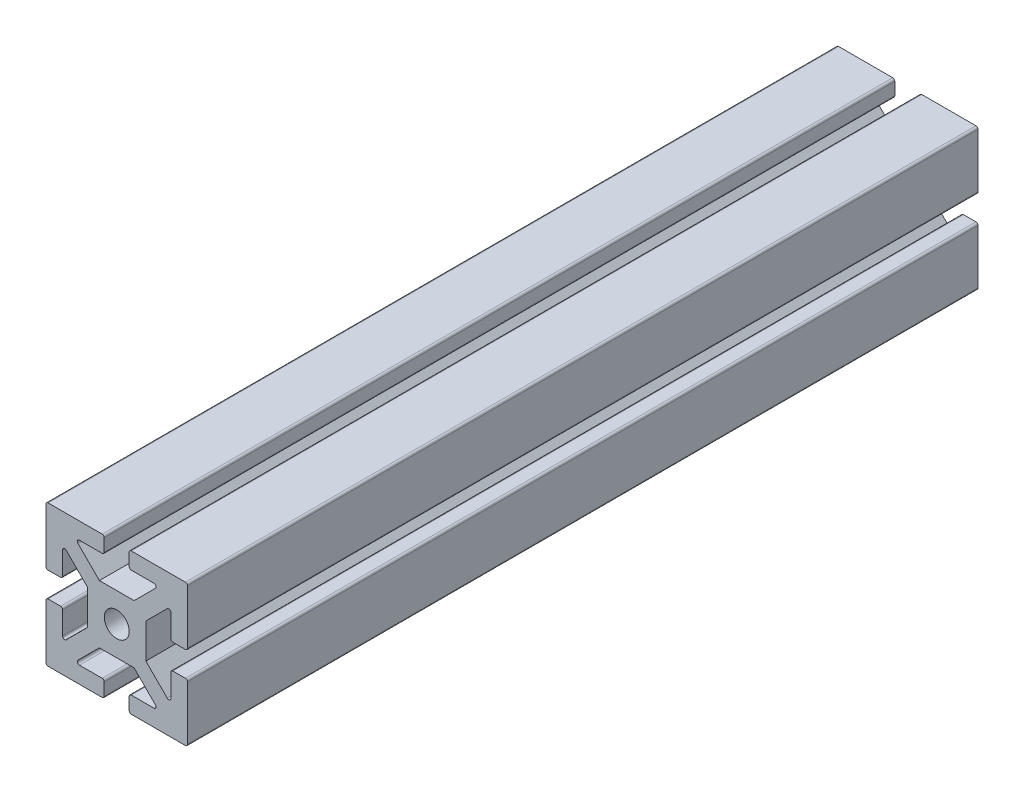
SolidWorks part; units mm, degrees
material "6061-T4 (SS)"
ref_plane "Front Plane" through (0, 0, 0) normal (0, 0, 1) x (1, 0, 0)
ref_plane "Top Plane" through (0, 0, 0) normal (0, 1, 0) x (1, 0, 0)
ref_plane "Right Plane" through (0, 0, 0) normal (1, 0, 0) x (0, 0, -1)
sketch "Sketch1" plane through (0, 0, 0) normal (0, 0, 1) x (1, 0, 0)
  line L0 (0, 0) -> (0, 14927.8117) construction
  line L1 (0, 0) -> (14927.8117, 0) construction
  line L2 (-2.0858, 3.5) -> (2.0858, 3.5)
  line L3 (2.0858, 3.5) -> (4.659, 6.0732)
  line L4 (4.4822, 6.5) -> (1.75, 6.5)
  line L5 (1.5, 6.75) -> (1.5, 8.25)
  line L6 (1.75, 8.5) -> (8.25, 8.5)
  line L7 (8.5, 8.25) -> (8.5, 1.75)
  line L8 (8.25, 1.5) -> (6.75, 1.5)
  line L9 (6.5, 1.75) -> (6.5, 4.4822)
  line L10 (6.0732, 4.659) -> (3.5, 2.0858)
  line L11 (3.5, 2.0858) -> (3.5, -2.0858)
  line L12 (6.0732, -4.659) -> (3.5, -2.0858)
  line L13 (6.5, -1.75) -> (6.5, -4.4822)
  line L14 (8.25, -1.5) -> (6.75, -1.5)
  line L15 (8.5, -8.25) -> (8.5, -1.75)
  line L16 (1.75, -8.5) -> (8.25, -8.5)
  line L17 (1.5, -6.75) -> (1.5, -8.25)
  line L18 (4.4822, -6.5) -> (1.75, -6.5)
  line L19 (2.0858, -3.5) -> (4.659, -6.0732)
  line L20 (-2.0858, -3.5) -> (2.0858, -3.5)
  line L21 (-2.0858, -3.5) -> (-4.659, -6.0732)
  line L22 (-4.4822, -6.5) -> (-1.75, -6.5)
  line L23 (-1.5, -6.75) -> (-1.5, -8.25)
  line L24 (-1.75, -8.5) -> (-8.25, -8.5)
  line L25 (-8.5, -8.25) -> (-8.5, -1.75)
  line L26 (-8.25, -1.5) -> (-6.75, -1.5)
  line L27 (-6.5, -1.75) -> (-6.5, -4.4822)
  line L28 (-6.0732, -4.659) -> (-3.5, -2.0858)
  line L29 (-3.5, 2.0858) -> (-3.5, -2.0858)
  line L30 (-6.0732, 4.659) -> (-3.5, 2.0858)
  line L31 (-6.5, 1.75) -> (-6.5, 4.4822)
  line L32 (-8.25, 1.5) -> (-6.75, 1.5)
  line L33 (-8.5, 8.25) -> (-8.5, 1.75)
  line L34 (-1.75, 8.5) -> (-8.25, 8.5)
  line L35 (-1.5, 6.75) -> (-1.5, 8.25)
  line L36 (-4.4822, 6.5) -> (-1.75, 6.5)
  line L37 (-2.0858, 3.5) -> (-4.659, 6.0732)
  circle A0 centre (0, 0) radius 1.5
  arc A1 (1.75, 6.5) -> (1.5, 6.75) centre (1.75, 6.75) cw
  arc A2 (1.5, 8.25) -> (1.75, 8.5) centre (1.75, 8.25) cw
  arc A3 (-1.75, 8.5) -> (-1.5, 8.25) centre (-1.75, 8.25) cw
  arc A4 (8.5, -8.25) -> (8.25, -8.5) centre (8.25, -8.25) cw
  arc A5 (8.25, -1.5) -> (8.5, -1.75) centre (8.25, -1.75) cw
  arc A6 (6.5, -1.75) -> (6.75, -1.5) centre (6.75, -1.75) cw
  arc A7 (6.0732, -4.659) -> (6.5, -4.4822) centre (6.25, -4.4822) ccw
  arc A8 (4.4822, -6.5) -> (4.659, -6.0732) centre (4.4822, -6.25) ccw
  arc A9 (1.75, -8.5) -> (1.5, -8.25) centre (1.75, -8.25) cw
  arc A10 (1.5, -6.75) -> (1.75, -6.5) centre (1.75, -6.75) cw
  arc A11 (-1.5, -8.25) -> (-1.75, -8.5) centre (-1.75, -8.25) cw
  arc A12 (-1.75, -6.5) -> (-1.5, -6.75) centre (-1.75, -6.75) cw
  arc A13 (-4.659, -6.0732) -> (-4.4822, -6.5) centre (-4.4822, -6.25) ccw
  arc A14 (-8.25, -8.5) -> (-8.5, -8.25) centre (-8.25, -8.25) cw
  arc A15 (-6.5, -4.4822) -> (-6.0732, -4.659) centre (-6.25, -4.4822) ccw
  arc A16 (-8.5, -1.75) -> (-8.25, -1.5) centre (-8.25, -1.75) cw
  arc A17 (-6.75, -1.5) -> (-6.5, -1.75) centre (-6.75, -1.75) cw
  arc A18 (-6.5, 1.75) -> (-6.75, 1.5) centre (-6.75, 1.75) cw
  arc A19 (-8.25, 1.5) -> (-8.5, 1.75) centre (-8.25, 1.75) cw
  arc A20 (-8.5, 8.25) -> (-8.25, 8.5) centre (-8.25, 8.25) cw
  arc A21 (-6.0732, 4.659) -> (-6.5, 4.4822) centre (-6.25, 4.4822) ccw
  arc A22 (-4.4822, 6.5) -> (-4.659, 6.0732) centre (-4.4822, 6.25) ccw
  arc A23 (-1.5, 6.75) -> (-1.75, 6.5) centre (-1.75, 6.75) cw
  arc A24 (4.659, 6.0732) -> (4.4822, 6.5) centre (4.4822, 6.25) ccw
  arc A25 (6.5, 4.4822) -> (6.0732, 4.659) centre (6.25, 4.4822) ccw
  arc A26 (6.75, 1.5) -> (6.5, 1.75) centre (6.75, 1.75) cw
  arc A27 (8.5, 1.75) -> (8.25, 1.5) centre (8.25, 1.75) cw
  arc A28 (8.25, 8.5) -> (8.5, 8.25) centre (8.25, 8.25) cw
  point P3 (-2.8019, 0.8886)
  point P19 (3.5, 0)
  point P29 (0, -3.5)
  point P46 (0, 3.5)
  point P49 (1.5, 6.5)
  point P52 (1.5, 8.5)
  point P55 (-1.5, 8.5)
  point P58 (8.5, -8.5)
  point P61 (8.5, -1.5)
  point P64 (6.5, -1.5)
  point P67 (6.5, -5.0858)
  point P70 (5.0858, -6.5)
  point P73 (1.5, -8.5)
  point P76 (1.5, -6.5)
  point P79 (-1.5, -8.5)
  point P82 (-1.5, -6.5)
  point P85 (-5.0858, -6.5)
  point P88 (-8.5, -8.5)
  point P91 (-6.5, -5.0858)
  point P94 (-8.5, -1.5)
  point P97 (-6.5, -1.5)
  point P100 (-6.5, 1.5)
  point P103 (-8.5, 1.5)
  point P106 (-8.5, 8.5)
  point P109 (-6.5, 5.0858)
  point P112 (-5.0858, 6.5)
  point P115 (-1.5, 6.5)
  point P118 (5.0858, 6.5)
  point P121 (6.5, 5.0858)
  point P124 (6.5, 1.5)
  point P127 (8.5, 1.5)
  point P130 (8.5, 8.5)
  point P131 (5.0714, -2.6287)
  point P132 (4.4538, -4.0482)
  point P133 (5.58, -2.8567)
  point P134 (4.7322, -2.9663)
  point P135 (4.8938, -2.9544)
  point P136 (5.4157, -2.9175)
  point P137 (7.3658, -5.75)
  dimension "D4" = 3
  dimension "D9" = 0.25
  dimension "D1" = 2
  dimension "D2" = 2
  dimension "D3" = 3
  dimension "D5" = 3.5
  dimension "D6" = 2
  dimension "D7" = 3
  dimension "D8" = 3
  dimension "D10" = 3.5
  dimension "D11" = 3
extrude "Boss-Extrude1" add sketch "Sketch1" along normal blind 95
equation "\"A\" = 2"
equation "\"B\" = 3"
equation "\"C\"= 95"
equation "\"D1@Sketch1\"=\"A\""
equation "\"D2@Sketch1\"=\"A\""
equation "\"D3@Sketch1\"=\"B\""
equation "\"D4@Sketch1\"=\"B\""
equation "\"D5@Sketch1\"=(\"B\"/2)+\"A\""
equation "\"D6@Sketch1\"=\"A\""
equation "\"D7@Sketch1\"=\"B\""
equation "\"D8@Sketch1\"=\"B\""
equation "\"D10@Sketch1\"=(\"B\"/2)+\"A\""
equation "\"D11@Sketch1\"=\"B\""
equation "\"D1@Boss-Extrude1\"=\"C\""
